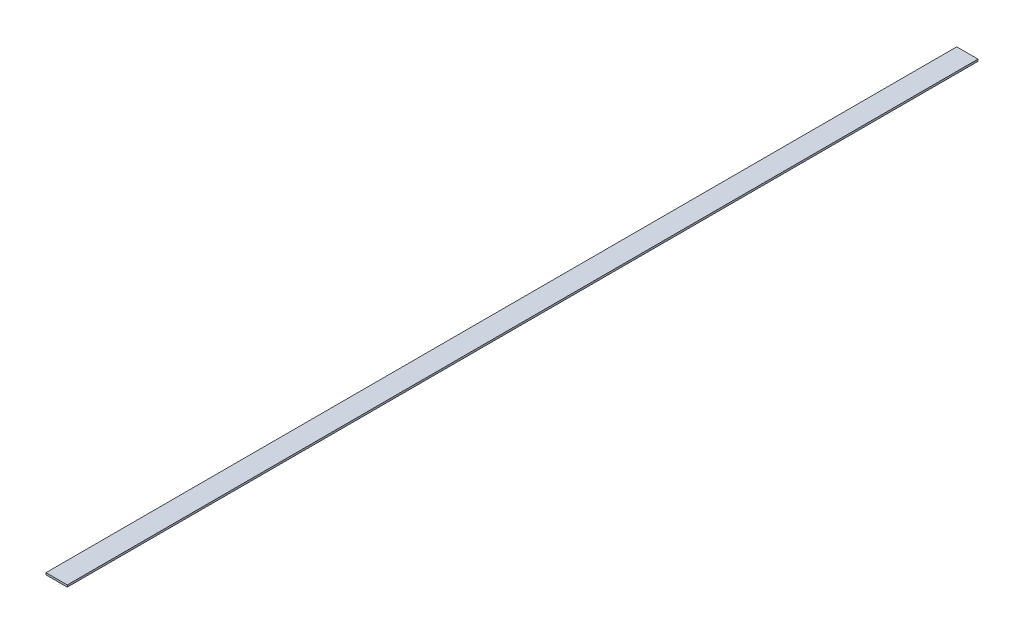
SolidWorks part; units mm, degrees
ref_plane "Front Plane" through (0, 0, 0) normal (0, 0, 1) x (1, 0, 0)
ref_plane "Top Plane" through (0, 0, 0) normal (0, 1, 0) x (1, 0, 0)
ref_plane "Right Plane" through (0, 0, 0) normal (1, 0, 0) x (0, 0, -1)
sketch "Sketch1" plane through (0, 0, 0) normal (0, 0, 1) x (1, 0, 0)
  line L1 (0, 0) -> (21.6, 0)
  line L2 (0, 0) -> (0, 2)
  line L3 (0, 2) -> (21.6, 2)
  line L4 (21.6, 0) -> (21.6, 2)
  dimension "D1" = 21.6
  dimension "D2" = 2
extrude "Boss-Extrude1" add sketch "Sketch1" along normal blind 925
equation "\"SlotWidth\"= 22mm"
equation "\"CarbonPaperThickness\"= 0.2mm"
equation "\"SpringThickness\"= 2mm"
equation "\"SpringWidth\"= \"SlotWidth\" - \"CarbonPaperThickness\" * 2"
equation "\"D1@Sketch1\"= \"SpringWidth\""
equation "\"D2@Sketch1\"= \"SpringThickness\""
equation "\"AxialLength\"= 925mm"
equation "\"D1@Boss-Extrude1\"= \"AxialLength\""
